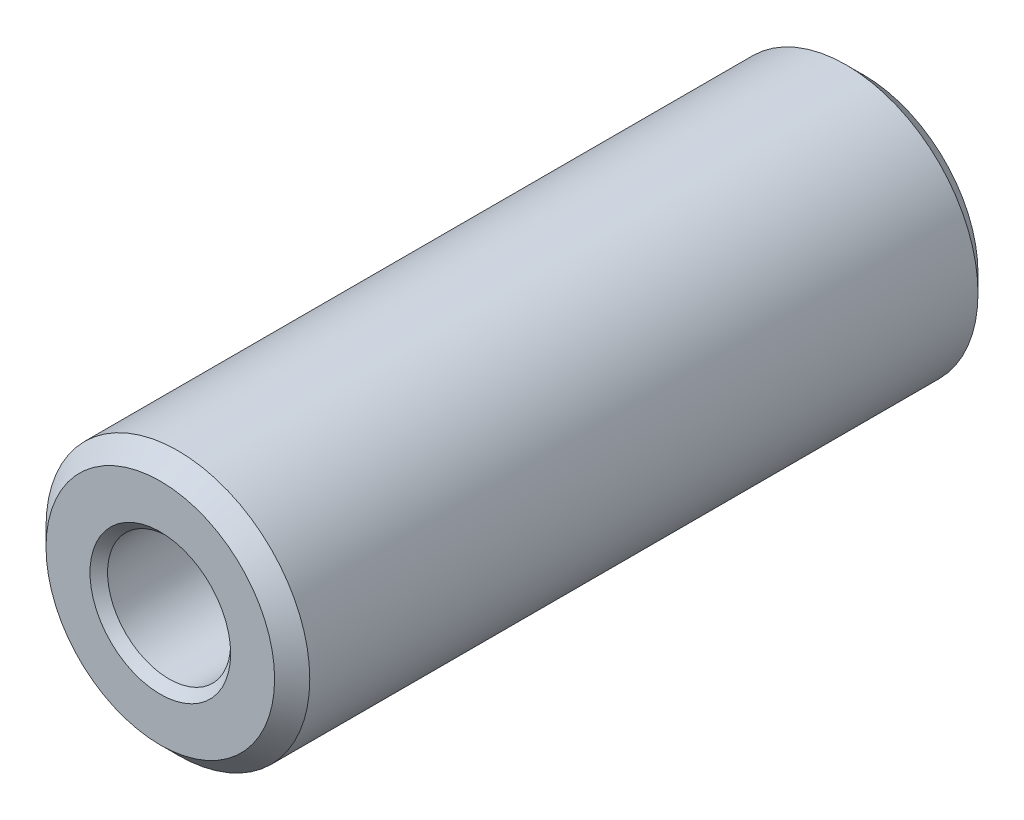
SolidWorks part; units mm, degrees
material "Ст3 ГОСТ 380-2005"
ref_plane "Спереди" through (0, 0, 0) normal (0, 0, 1) x (1, 0, 0)
ref_plane "Сверху" through (0, 0, 0) normal (0, 1, 0) x (1, 0, 0)
ref_plane "Справа" through (0, 0, 0) normal (1, 0, 0) x (0, 0, -1)
sketch "Эскиз1" plane through (0, 0, 0) normal (0, 0, 1) x (1, 0, 0)
  circle A0 centre (0, 0) radius 15
  circle A1 centre (0, 0) radius 7
  dimension "D1" = 30
  dimension "D2" = 14
extrude "Бобышка-Вытянуть1" add sketch "Эскиз1" along normal blind 80
chamfer "Фаска1" distance 1 angle 45 2 edges at (7, 0, 0) (7, 0, 80)
chamfer "Фаска2" distance 2 angle 45 2 edges at (15, 0, 0) (15, 0, 80)
